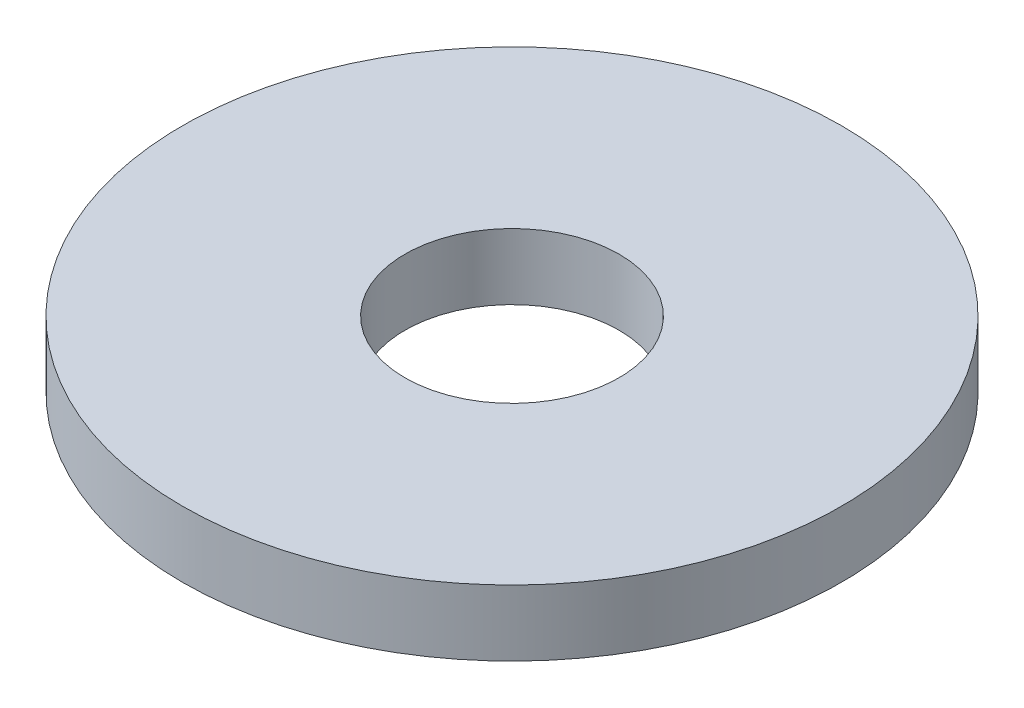
SolidWorks part; units mm, degrees
ref_plane "Plan de face" through (0, 0, 0) normal (0, 0, 1) x (1, 0, 0)
ref_plane "Plan de dessus" through (0, 0, 0) normal (0, 1, 0) x (1, 0, 0)
ref_plane "Plan de droite" through (0, 0, 0) normal (1, 0, 0) x (0, 0, -1)
sketch "Esquisse1" plane through (0, 0, 0) normal (0, 1, 0) x (1, 0, 0)
  circle A0 centre (0, 0) radius 3.25
  circle A1 centre (0, 0) radius 10
  dimension "D1" = 6.5
  dimension "D2" = 20
extrude "Boss.-Extru.1" add sketch "Esquisse1" along normal blind 2
